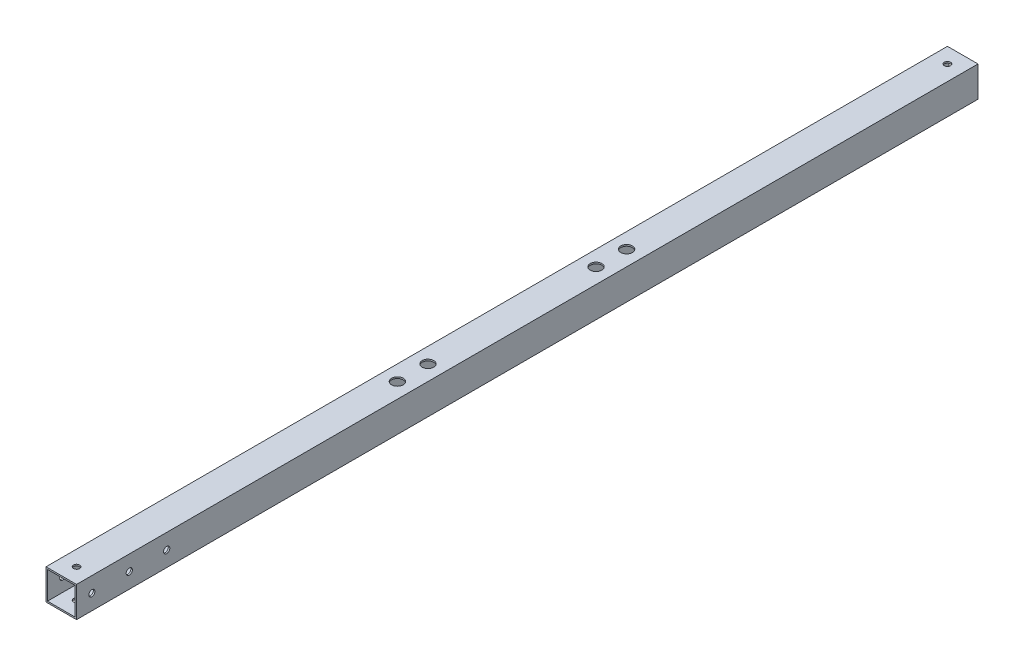
SolidWorks part; units mm, degrees
material "6063-T5"
ref_plane "前视基准面" through (0, 0, 0) normal (0, 0, 1) x (1, 0, 0)
ref_plane "上视基准面" through (0, 0, 0) normal (0, 1, 0) x (1, 0, 0)
ref_plane "右视基准面" through (0, 0, 0) normal (1, 0, 0) x (0, 0, -1)
sketch "草图1" plane through (0, 0, 0) normal (0, 0, 1) x (1, 0, 0)
  line L0 (-9, -9) -> (-9, 9)
  line L1 (-10, -10) -> (10, -10)
  line L2 (-10, -10) -> (-10, 10)
  line L3 (-10, 10) -> (10, 10)
  line L4 (10, -10) -> (10, 10)
  line L5 (0, 10) -> (0, -10) construction
  line L6 (-10, 0) -> (10, 0) construction
  line L7 (-9, 9) -> (9, 9)
  line L8 (9, -9) -> (9, 9)
  line L9 (-9, -9) -> (9, -9)
  point P0 (0, 0)
  dimension "D1" = 20
  dimension "D2" = 1
extrude "凸台-拉伸1" add sketch "草图1" along normal mid plane 590
sketch "草图2" plane through (0, 10, 0) normal (0, 1, 0) x (1, 0, 0)
  circle A0 centre (0, -75) radius 2.025 construction
  circle A1 centre (0, -55) radius 2.025 construction
  circle A2 centre (0, 55) radius 2.025 construction
  circle A3 centre (0, 75) radius 2.025 construction
  circle A4 centre (0, -75) radius 2.025
  circle A5 centre (0, -55) radius 2.025
  circle A6 centre (0, 55) radius 2.025
  circle A7 centre (0, 75) radius 2.025
extrude "切除-拉伸1" cut sketch "草图2" against normal mid plane 90
sketch "草图3" plane through (0, 10, 0) normal (0, 1, 0) x (1, 0, 0)
  circle A0 centre (0, 75) radius 3.8
  circle A1 centre (0, 55) radius 3.8
  circle A2 centre (0, -55) radius 3.8
  circle A3 centre (0, -75) radius 3.8
  dimension "D1" = 7.6
extrude "切除-拉伸2" cut sketch "草图3" against normal mid plane 10
sketch "草图4" plane through (10, 0, 0) normal (1, 0, 0) x (0, 0, -1)
  circle A0 centre (-236, 0) radius 2.025 construction
  circle A1 centre (-260.5, 0) radius 2.025 construction
  circle A2 centre (-285, 0) radius 2.025 construction
  circle A3 centre (-236, 0) radius 2.025
  circle A4 centre (-260.5, 0) radius 2.025
  circle A5 centre (-285, 0) radius 2.025
extrude "切除-拉伸3" cut sketch "草图4" against normal blind 73
sketch "草图5" [suppressed] plane through (-10, 0, 0) normal (-1, 0, 0) x (0, 0, 1)
  circle A0 centre (38, 0) radius 2.025 construction
  circle A1 centre (13.5, 0) radius 2.025 construction
  circle A2 centre (38, 0) radius 2.025
  circle A3 centre (13.5, 0) radius 2.025
extrude "切除-拉伸4" [suppressed] cut sketch "草图5" against normal up to surface (20 mm away)
sketch "草图6" [suppressed] plane through (0, 10, 0) normal (0, 1, 0) x (1, 0, 0)
  circle A0 centre (0, 42.5) radius 2.025 construction
  circle A1 centre (0, 8.5) radius 2.025 construction
  circle A2 centre (0, 42.5) radius 2.025
  circle A3 centre (0, 8.5) radius 2.025
extrude "切除-拉伸5" [suppressed] cut sketch "草图6" against normal blind 80
sketch "草图7" [suppressed] plane through (0, 10, 0) normal (0, 1, 0) x (1, 0, 0)
  circle A0 centre (0, -62.75) radius 2.025 construction
  circle A1 centre (0, 53.75) radius 2.025 construction
  circle A2 centre (0, -62.75) radius 2.025
  circle A3 centre (0, 53.75) radius 2.025
extrude "切除-拉伸6" [suppressed] cut sketch "草图7" against normal blind 80
sketch "草图8" [suppressed] plane through (0, 9, 0) normal (0, -1, 0) x (1, 0, 0)
  circle A0 centre (0, -33.75) radius 2.025 construction
  circle A1 centre (0, -5.75) radius 2.025 construction
  circle A2 centre (0, -33.75) radius 2.025
  circle A3 centre (0, -5.75) radius 2.025
extrude "切除-拉伸7" [suppressed] cut sketch "草图8" against normal blind 60
sketch "草图9" [suppressed] plane through (0, -9, 0) normal (0, 1, 0) x (1, 0, 0)
  circle A0 centre (0, 33.75) radius 3.9
  circle A1 centre (0, 5.75) radius 3.9
  dimension "D1" = 7.8
extrude "切除-拉伸8" [suppressed] cut sketch "草图9" against normal blind 10
sketch "草图10" [suppressed] plane through (-10, 0, 0) normal (-1, 0, 0) x (0, 0, 1)
  circle A0 centre (-4.75, 0) radius 2.025 construction
  circle A1 centre (-34.75, 0) radius 2.025 construction
  circle A2 centre (-4.75, 0) radius 2.025
  circle A3 centre (-34.75, 0) radius 2.025
extrude "切除-拉伸9" [suppressed] cut sketch "草图10" against normal up to surface (20 mm away)
sketch "草图11" [suppressed] plane through (0, 10, 0) normal (0, 1, 0) x (1, 0, 0)
  circle A0 centre (0, -137.5) radius 1.75 construction
  circle A1 centre (0, -137.5) radius 1.75 construction
  circle A2 centre (0, -137.5) radius 1.525
  dimension "D1" = 3.05
extrude "切除-拉伸10" [suppressed] cut sketch "草图11" against normal blind 10
pattern_linear "阵列(线性)1" [suppressed] count 10 spacing 30
sketch "草图12" [suppressed] plane through (0, -10, 0) normal (0, -1, 0) x (1, 0, 0)
  circle A0 centre (0, -144.5) radius 2.025 construction
  circle A1 centre (0, -124.5) radius 2.025 construction
  circle A2 centre (0, -144.5) radius 2.025
  circle A3 centre (0, -124.5) radius 2.025
extrude "切除-拉伸11" [suppressed] cut sketch "草图12" against normal blind 10
mirror "镜向1" [suppressed] about plane through (0, 0, 0) normal (0, 0, 1)
sketch "草图13" [suppressed] plane through (10, 0, 0) normal (1, 0, 0) x (0, 0, -1)
  circle A0 centre (144.5, 0) radius 2.025 construction
  circle A1 centre (119.5, 0) radius 2.025 construction
  circle A2 centre (-154.5, 0) radius 2.025 construction
  circle A3 centre (-124.5, 0) radius 2.025 construction
  circle A4 centre (144.5, 0) radius 2.025
  circle A5 centre (119.5, 0) radius 2.025
  circle A6 centre (-154.5, 0) radius 2.025
  circle A7 centre (-124.5, 0) radius 2.025
extrude "切除-拉伸12" [suppressed] cut sketch "草图13" against normal blind 60
sketch "草图14" [suppressed] plane through (0, -9, 0) normal (0, 1, 0) x (1, 0, 0)
  circle A0 centre (0, 102.5) radius 3.8
  dimension "D1" = 7.6
extrude "切除-拉伸13" [suppressed] cut sketch "草图14" against normal blind 60
pattern_linear "阵列(线性)2" [suppressed] count 8 spacing 30
sketch "草图15" plane through (0, -10, 0) normal (0, -1, 0) x (1, 0, 0)
  line L0 (-10, 275) -> (10, 275) construction
  line L1 (-10, 295) -> (-10, -295) construction
  line L2 (10, 295) -> (10, -295) construction
  line L3 (-10, 295) -> (10, 295) construction
  line L4 (-10, 295) -> (10, 275) construction
  circle A0 centre (0, 285) radius 2.025
  dimension "D2" = 4.05
  dimension "D1" = 20
extrude "切除-拉伸14" cut sketch "草图15" against normal blind 70
mirror "镜向2" about plane through (0, 0, 0) normal (0, 0, 1) of "切除-拉伸14"
sketch "草图16" [suppressed] plane through (-10, 0, 0) normal (-1, 0, 0) x (0, 0, 1)
  line L0 (-87.75, 10) -> (-87.75, -10) construction
  line L1 (-77.75, 0) -> (0, 0) construction
  circle A1 centre (81.75, 0) radius 2.025 construction
  circle A2 centre (63.75, 0) radius 2.025 construction
  circle A3 centre (-77.75, 0) radius 2.025
  circle A4 centre (81.75, 0) radius 2.025
  circle A5 centre (63.75, 0) radius 2.025
  dimension "D1" = 10
extrude "切除-拉伸15" [suppressed] cut sketch "草图16" against normal blind 10
sketch "草图17" [suppressed] plane through (9, 0, 0) normal (-1, 0, 0) x (0, 0, 1)
  circle A0 centre (-77.75, 0) radius 3.9
  circle A1 centre (63.75, 0) radius 3.9
  circle A2 centre (81.75, 0) radius 3.9
  dimension "D1" = 7.8
extrude "切除-拉伸16" [suppressed] cut sketch "草图17" against normal blind 10
sketch "草图18" [suppressed] plane through (0, 10, 0) normal (0, 1, 0) x (1, 0, 0)
  circle A0 centre (0, -53.75) radius 2.025 construction
  circle A1 centre (0, 62.75) radius 2.025 construction
  circle A2 centre (0, -53.75) radius 2.025
  circle A3 centre (0, 62.75) radius 2.025
extrude "切除-拉伸17" [suppressed] cut sketch "草图18" against normal blind 60
sketch "草图19" [suppressed] plane through (10, 0, 0) normal (1, 0, 0) x (0, 0, -1)
  circle A0 centre (50.75, 0) radius 1.525 construction
  circle A1 centre (74.75, 0) radius 1.525 construction
  circle A2 centre (50.75, 0) radius 1.525
  circle A3 centre (74.75, 0) radius 1.525
extrude "切除-拉伸18" [suppressed] cut sketch "草图19" against normal blind 60
sketch "草图20" [suppressed] plane through (10, 0, 0) normal (1, 0, 0) x (0, 0, -1)
  circle A0 centre (-50.75, 0) radius 1.525 construction
  circle A1 centre (-74.75, 0) radius 1.525 construction
  circle A2 centre (-50.75, 0) radius 1.525
  circle A3 centre (-74.75, 0) radius 1.525
extrude "切除-拉伸19" [suppressed] cut sketch "草图20" against normal blind 70
sketch "草图21" [suppressed] plane through (0, -10, 0) normal (0, -1, 0) x (1, 0, 0)
  circle A0 centre (0, 9.225) radius 1.525 construction
  circle A1 centre (0, -9.225) radius 1.525 construction
  circle A2 centre (0, 9.225) radius 1.525
  circle A3 centre (0, -9.225) radius 1.525
extrude "切除-拉伸20" [suppressed] cut sketch "草图21" against normal blind 30
sketch "草图22" [suppressed] plane through (-9, 0, 0) normal (1, 0, 0) x (0, 0, -1)
  line L0 (13.225, 0) -> (-13.225, 0) construction
  line L1 (13.225, 9) -> (13.225, -9) construction
  line L2 (-13.225, 9) -> (-13.225, -9) construction
  circle A0 centre (9.225, 0) radius 1.525
  circle A1 centre (-9.225, 0) radius 1.525
  dimension "D3" = 3.05
  dimension "D1" = 4
  dimension "D2" = 4
extrude "切除-拉伸21" [suppressed] cut sketch "草图22" against normal blind 30
sketch "草图25" [suppressed] plane through (0, 10, 0) normal (0, 1, 0) x (1, 0, 0)
  line L0 (10, -225) -> (-10, -225) construction
  line L1 (0, -134.5) -> (0, -225) construction
  line L2 (0, 0) -> (37.677, 0) construction
  circle A0 centre (0, -134.5) radius 1.525
  circle A1 centre (0, 134.5) radius 1.525
  dimension "D1" = 3.05
  dimension "D2" = 90.5
extrude "切除-拉伸22" [suppressed] cut sketch "草图25" against normal blind 46
sketch "草图26" [suppressed] plane through (0, 10, 0) normal (0, 1, 0) x (1, 0, 0)
  line L0 (0, 0) -> (24.0127, 0) construction
  circle A0 centre (0, -134.5) radius 3.8
  circle A1 centre (0, 134.5) radius 3.8
  dimension "D1" = 7.6
extrude "切除-拉伸23" [suppressed] cut sketch "草图26" against normal blind 10
sketch "草图27" [suppressed] plane through (10, 0, 0) normal (1, 0, 0) x (0, 0, -1)
  line L0 (0, 0) -> (0, -25.4602) construction
  circle A0 centre (-100.5, -1.5) radius 2.025 construction
  circle A1 centre (-134.5, -1.5) radius 2.025 construction
  circle A2 centre (-168.5, -1.5) radius 2.025 construction
  circle A3 centre (-100.5, -1.5) radius 2.025
  circle A4 centre (-134.5, -1.5) radius 2.025
  circle A5 centre (-168.5, -1.5) radius 2.025
  circle A6 centre (168.5, -1.5) radius 2.025
  circle A7 centre (134.5, -1.5) radius 2.025
  circle A8 centre (100.5, -1.5) radius 2.025
extrude "切除-拉伸24" [suppressed] cut sketch "草图27" against normal blind 10
sketch "草图28" [suppressed] plane through (0, 10, 0) normal (0, 1, 0) x (1, 0, 0)
  line L0 (0, 15) -> (0, -15) construction
  circle A0 centre (0, 15) radius 1.525
  circle A1 centre (0, -15) radius 1.525
  point P4 (0, 0)
  dimension "D1" = 3.05
  dimension "D2" = 30
extrude "切除-拉伸25" [suppressed] cut sketch "草图28" against normal blind 28
sketch "草图29" [suppressed] plane through (0, -10, 0) normal (0, -1, 0) x (1, 0, 0)
  circle A0 centre (0, 15) radius 3.35
  circle A1 centre (0, -15) radius 3.35
  dimension "D1" = 6.7
extrude "切除-拉伸26" [suppressed] cut sketch "草图29" against normal blind 10
sketch "草图30" [suppressed] plane through (0, 10, 0) normal (0, 1, 0) x (1, 0, 0)
  line L0 (0, 0) -> (0, 26.25) construction
  line L1 (0, 26.25) -> (0, 41.25) construction
  line L2 (-5, 26.25) -> (-5, 41.25)
  line L3 (5, 26.25) -> (5, 41.25)
  line L4 (0, 0) -> (18.3063, 0) construction
  line L5 (0, -26.25) -> (0, -41.25) construction
  line L6 (-5, -26.25) -> (-5, -41.25)
  line L7 (5, -26.25) -> (5, -41.25)
  arc A0 (-5, 26.25) -> (5, 26.25) centre (0, 26.25) ccw
  arc A1 (5, 41.25) -> (-5, 41.25) centre (0, 41.25) ccw
  arc A2 (-5, -26.25) -> (5, -26.25) centre (0, -26.25) cw
  arc A3 (5, -41.25) -> (-5, -41.25) centre (0, -41.25) cw
  point P3 (0, 33.75)
  point P12 (0, -33.75)
  dimension "D3" = 15
  dimension "D1" = 67.5
  dimension "D2" = 10
extrude "切除-拉伸27" [suppressed] cut sketch "草图30" against normal blind 54
sketch "草图31" [suppressed] plane through (-10, 0, 0) normal (-1, 0, 0) x (0, 0, 1)
  line L0 (134.8, -6) -> (154.8, -6) construction
  line L2 (225, 10) -> (225, -10) construction
  line L3 (225, -10) -> (-225, -10) construction
  line L4 (0, 0) -> (0, 36.8399) construction
  line L5 (-134.8, -6) -> (-154.8, -6) construction
  circle A0 centre (154.8, -6) radius 1.525
  circle A1 centre (134.8, -6) radius 1.525
  circle A2 centre (-134.8, -6) radius 1.525
  circle A3 centre (-154.8, -6) radius 1.525
  dimension "D3" = 3.05
  dimension "D1" = 20
  dimension "D2" = 70.2
  dimension "D4" = 4
extrude "切除-拉伸28" [suppressed] cut sketch "草图31" against normal blind 50
sketch "草图32" [suppressed] plane through (10, 0, 0) normal (1, 0, 0) x (0, 0, -1)
  line L0 (-145, -6) -> (-125, -6) construction
  line L1 (-135, -6) -> (-135, -15.3787) construction
  line L2 (-147, 0) -> (-225, 0) construction
  line L3 (-225, -10) -> (-225, 10) construction
  line L4 (0, 0) -> (0, -37.3608) construction
  circle A1 centre (-147, 0) radius 6
  circle A2 centre (-123, 0) radius 6
  circle A3 centre (123, 0) radius 6
  circle A4 centre (147, 0) radius 6
  dimension "D1" = 12
  dimension "D2" = 12
extrude "切除-拉伸29" [suppressed] cut sketch "草图32" against normal blind 3
sketch "草图33" [suppressed] plane through (0, 10, 0) normal (0, 1, 0) x (1, 0, 0)
  line L0 (6, -164.5) -> (6, -184.5) construction
  line L1 (10, -225) -> (-10, -225) construction
  line L2 (10, -225) -> (10, 225) construction
  line L3 (0, 0) -> (43.4029, 0) construction
  circle A0 centre (6, -184.5) radius 1.525
  circle A1 centre (6, -164.5) radius 1.525
  circle A2 centre (6, 184.5) radius 1.525
  circle A3 centre (6, 164.5) radius 1.525
  point P3 (6, -174.5)
  dimension "D4" = 3.05
  dimension "D1" = 20
  dimension "D2" = 40.5
  dimension "D3" = 4
extrude "切除-拉伸30" [suppressed] cut sketch "草图33" against normal blind 10
sketch "草图34" [suppressed] plane through (10, 0, 0) normal (1, 0, 0) x (0, 0, -1)
  line L0 (0, 0) -> (0, 41.5364) construction
  circle A0 centre (174.5, 6) radius 1.25 construction
  circle A1 centre (194.5, 6) radius 1.25 construction
  circle A2 centre (174.5, 6) radius 1.25 construction
  circle A3 centre (194.5, 6) radius 1.25 construction
  circle A4 centre (194.5, 6) radius 1.525
  circle A5 centre (174.5, 6) radius 1.525
  circle A6 centre (-194.5, 6) radius 1.25 construction
  circle A7 centre (-174.5, 6) radius 1.25 construction
  circle A8 centre (-174.5, 6) radius 1.525
  circle A9 centre (-194.5, 6) radius 1.525
  dimension "D1" = 3.05
extrude "切除-拉伸31" [suppressed] cut sketch "草图34" against normal blind 10
sketch "草图35" [suppressed] plane through (0, -9, 0) normal (0, 1, 0) x (1, 0, 0)
  line L0 (6, 144.7955) -> (-6, 144.7955) construction
  line L1 (0, 0) -> (22.3107, 0) construction
  line L2 (-6, 144.7955) -> (-6, 124.7955) construction
  line L3 (-6, 124.7955) -> (6, 124.7955) construction
  line L4 (6, 124.7955) -> (6, 144.7955) construction
  line L5 (0, 144.7955) -> (0, -144.7955) construction
  line L6 (6, -124.7955) -> (6, -144.7955) construction
  line L7 (-6, -124.7955) -> (6, -124.7955) construction
  line L8 (-6, -144.7955) -> (-6, -124.7955) construction
  line L9 (6, -144.7955) -> (-6, -144.7955) construction
  circle A0 centre (6, -144.7955) radius 1.25 construction
  circle A1 centre (6, -124.7955) radius 1.25 construction
  circle A2 centre (-6, 144.7955) radius 1.25 construction
  circle A3 centre (-6, 124.7955) radius 1.25 construction
  circle A6 centre (-6, 144.7955) radius 1.525
  circle A7 centre (-6, 124.7955) radius 1.525
  circle A8 centre (6, 124.7955) radius 1.25 construction
  circle A9 centre (6, 144.7955) radius 1.25 construction
  circle A10 centre (6, 124.7955) radius 1.525
  circle A11 centre (6, 144.7955) radius 1.525
  circle A12 centre (-6, -124.7955) radius 1.25 construction
  circle A13 centre (-6, -144.7955) radius 1.25 construction
  circle A14 centre (6, -144.7955) radius 1.525
  circle A15 centre (6, -124.7955) radius 1.525
  circle A16 centre (-6, -124.7955) radius 1.525
  circle A17 centre (-6, -144.7955) radius 1.525
  dimension "D1" = 3.05
  dimension "D2" = 12
  dimension "D3" = 20
  dimension "D4" = 144.7955
extrude "切除-拉伸32" [suppressed] cut sketch "草图35" against normal blind 10 contours A6 | A11 | A7 | A10 | A16 | A15 | A17 | A14
sketch "草图36" [suppressed] plane through (10, 0, 0) normal (1, 0, 0) x (0, 0, -1)
  line L0 (-225, -10) -> (225, -10) construction
  line L1 (-161.8584, -10) -> (161.8584, -10)
  line L2 (-161.8584, -10) -> (-161.8584, -4)
  line L3 (-161.8584, -4) -> (161.8584, -4)
  line L4 (161.8584, -10) -> (161.8584, -4)
  line L5 (0, 0) -> (0, -4) construction
  dimension "D1" = 6
  dimension "D2" = 323.7169
extrude "凸台-拉伸2" [suppressed] add sketch "草图36" against normal blind 1
sketch "草图37" [suppressed] plane through (10, 0, 0) normal (1, 0, 0) x (0, 0, -1)
  circle A0 centre (56.2617, 0) radius 7.7071
  circle A1 centre (40.2169, 0) radius 7.2735
sketch "草图38" [suppressed] plane through (10, 0, 0) normal (1, 0, 0) x (0, 0, -1)
  line L0 (77.75, -10) -> (77.75, 10) construction
  circle A0 centre (36.75, 0) radius 2.525
  circle A1 centre (16.75, 0) radius 2.525
  dimension "D1" = 5.05
  dimension "D2" = 20
  dimension "D3" = 41
extrude "切除-拉伸33" [suppressed] cut sketch "草图38" against normal through all both and the other way through all
sketch "草图39" [suppressed] plane through (10, 0, 0) normal (1, 0, 0) x (0, 0, -1)
  line L0 (-77.75, -10) -> (-77.75, 10) construction
  circle A0 centre (-16.75, 0) radius 2.525
  circle A1 centre (-36.75, 0) radius 2.525
  dimension "D1" = 5.05
  dimension "D2" = 20
  dimension "D3" = 41
extrude "切除-拉伸34" [suppressed] cut sketch "草图39" against normal through all both
sketch "草图40" [suppressed] plane through (10, 0, 0) normal (1, 0, 0) x (0, 0, -1)
  line L0 (77.75, -10) -> (77.75, 10) construction
  circle A0 centre (40, 0) radius 2.025
  dimension "D1" = 4.05
  dimension "D2" = 37.75
extrude "切除-拉伸35" [suppressed] cut sketch "草图40" against normal through all both and the other way through all
sketch "草图41" [suppressed] plane through (10, 0, 0) normal (1, 0, 0) x (0, 0, -1)
  line L0 (-77.75, -10) -> (-77.75, 10) construction
  circle A0 centre (-40, 0) radius 2.025
  dimension "D1" = 4.05
  dimension "D2" = 37.75
extrude "切除-拉伸36" [suppressed] cut sketch "草图41" against normal through all both and the other way through all
equation "\"D2@草图22\"=\"D1@草图22\""
